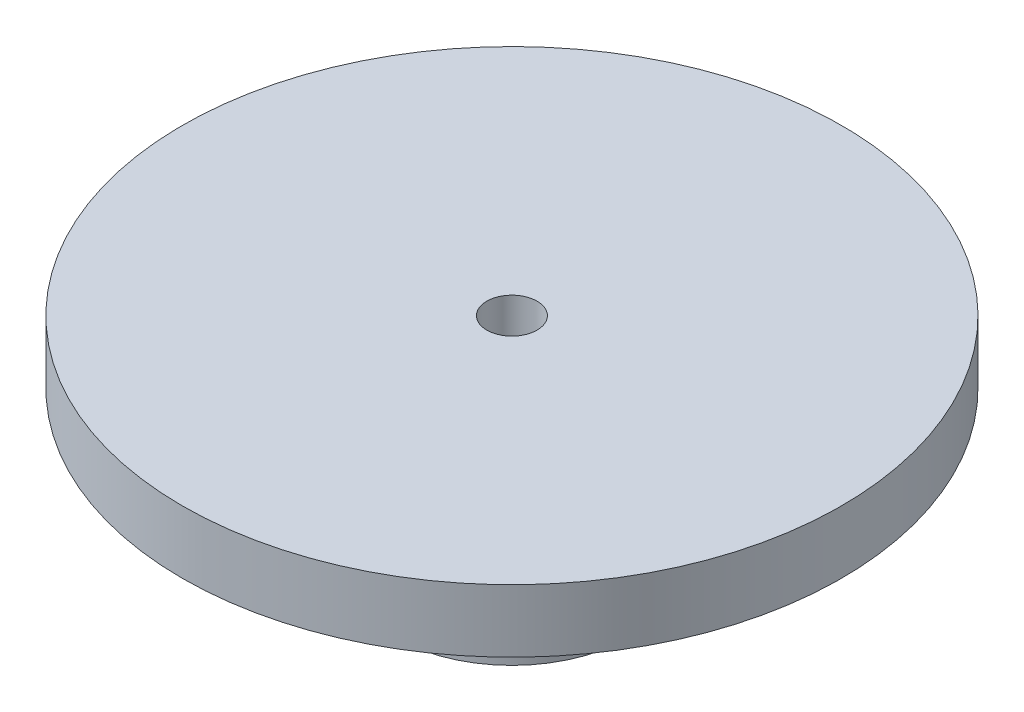
SolidWorks part; units mm, degrees
ref_plane "Alzado" through (0, 0, 0) normal (0, 0, 1) x (1, 0, 0)
ref_plane "Planta" through (0, 0, 0) normal (0, 1, 0) x (1, 0, 0)
ref_plane "Vista lateral" through (0, 0, 0) normal (1, 0, 0) x (0, 0, -1)
sketch "Croquis1" plane through (0, 0, 0) normal (0, 1, 0) x (1, 0, 0)
  circle A0 centre (0, 0) radius 3
  circle A1 centre (0, 0) radius 3.75
  dimension "D1" = 6
  dimension "D2" = 7.5
extrude "Saliente-Extruir1" add sketch "Croquis1" along normal blind 5
sketch "Croquis2" plane through (0, 5, 0) normal (0, 1, 0) x (1, 0, 0)
  circle A0 centre (0, 0) radius 10.5
  circle A1 centre (0, 0) radius 0.8
  dimension "D1" = 21
extrude "Saliente-Extruir2" add sketch "Croquis2" along normal blind 2
